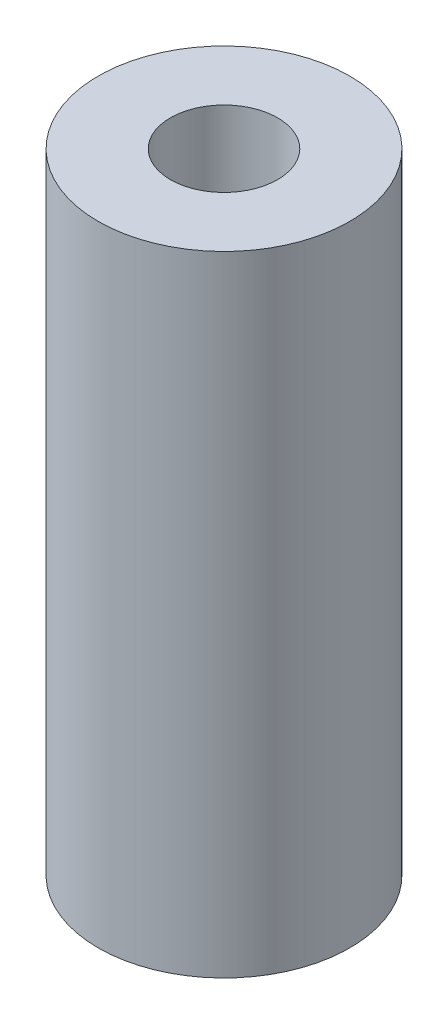
SolidWorks part; units mm, degrees
ref_plane "Front Plane" through (0, 0, 0) normal (0, 0, 1) x (1, 0, 0)
ref_plane "Top Plane" through (0, 0, 0) normal (0, 1, 0) x (1, 0, 0)
ref_plane "Right Plane" through (0, 0, 0) normal (1, 0, 0) x (0, 0, -1)
sketch "Sketch1" plane through (0, 0, 0) normal (0, 1, 0) x (1, 0, 0)
  circle A0 centre (0, 0) radius 3.175
  dimension "D1" = 6.35
extrude "Boss-Extrude1" add sketch "Sketch1" along normal blind 15.875
hole_wizard "Tap Drill for #6-32 Tap1" positions "Sketch3" profile "Sketch2" hole size "#6-32" standard "ANSI Inch" end condition through all
sketch "Sketch3" plane through (0, 15.875, 0) normal (0, 1, 0) x (1, 0, 0)
  point P0 (0, 0)
sketch "Sketch2" plane through (0, 15.875, 0) normal (1, 0, 0) x (0, 0, 1)
  line L0 (0, 0) -> (0, 15.875)
  line L1 (0, 15.875) -> (1.3525, 15.875)
  line L2 (1.3525, 15.875) -> (1.3525, 0)
  line L5 (1.3525, 0) -> (0, 0)
  line L11 (0, -6.35) -> (0, 107.95) construction
  dimension "Thru Hole Dia." = 2.7051
  dimension "Thru Hole Depth" = 15.875
